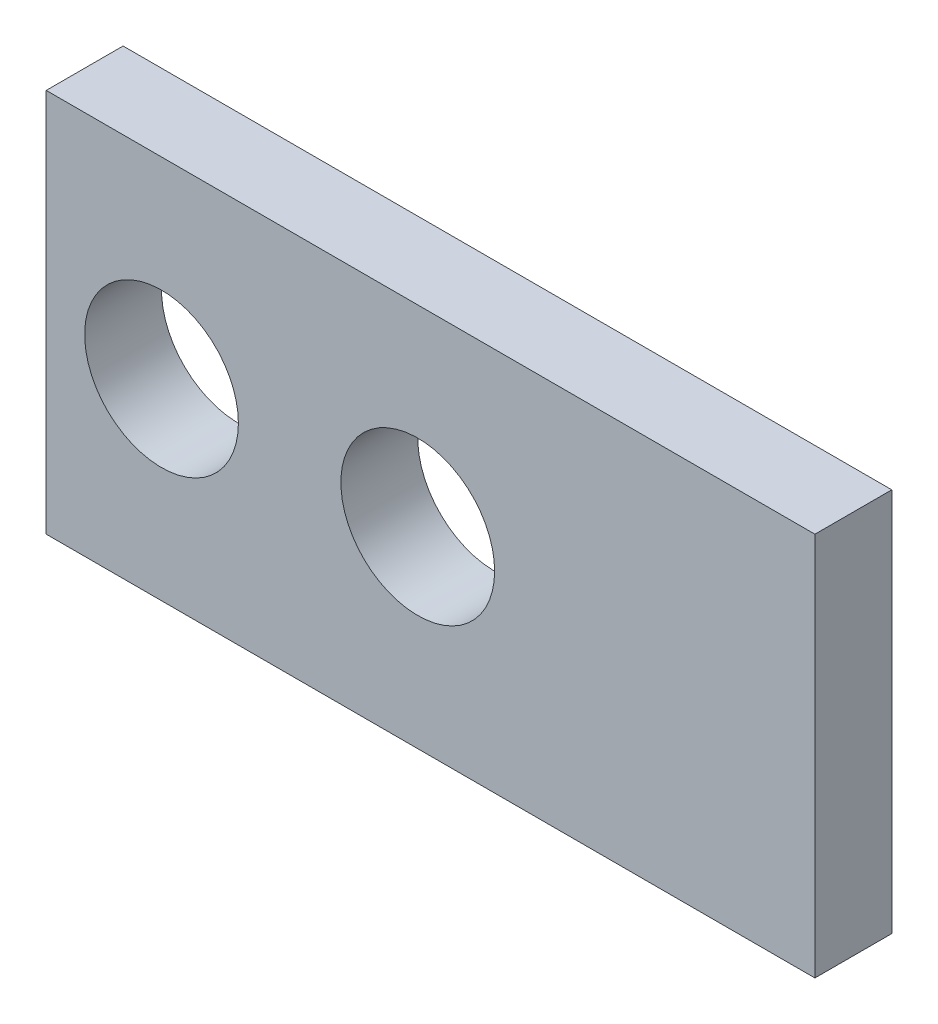
SolidWorks part; units mm, degrees
ref_plane "Piano frontale" through (0, 0, 0) normal (0, 0, 1) x (1, 0, 0)
ref_plane "Piano superiore" through (0, 0, 0) normal (0, 1, 0) x (1, 0, 0)
ref_plane "Piano destro" through (0, 0, 0) normal (1, 0, 0) x (0, 0, -1)
sketch "Sketch1" plane through (0, 0, 0) normal (0, 0, 1) x (1, 0, 0)
  line L1 (-50, -25) -> (50, -25)
  line L2 (-50, -25) -> (-50, 25)
  line L3 (-50, 25) -> (50, 25)
  line L4 (50, -25) -> (50, 25)
  line L5 (-50, -25) -> (50, 25) construction
  line L6 (-50, 25) -> (50, -25) construction
  point P0 (0, 0)
extrude "Boss-Extrude1" add sketch "Sketch1" along normal blind 10
hole_wizard "Ø20.0mm Dowel Slot1" positions "Sketch3" profile "Sketch2" size "Ø20.0" standard "ANSI Metric" slot yes
sketch "Sketch3" plane through (0, 0, 10) normal (0, 0, 1) x (1, 0, 0)
  line L0 (-50, 25) -> (-50, -25) construction
  line L1 (5.5, 0) -> (-5.5, 0) construction
  point P0 (-35, 0)
  dimension "D1" = 15
sketch "Sketch2" plane through (-35, 0, 10) normal (1, 0, 0) x (0, -1, 0)
  line L0 (0, 0) -> (0, 16.0086)
  line L1 (0, 16.0086) -> (10, 10)
  line L2 (10, 10) -> (10, 0)
  line L5 (10, 0) -> (0, 0)
  line L10 (0, 16.0086) -> (-10, 10) construction
  line L11 (0, -6.35) -> (0, 107.95) construction
  dimension "Hole Dia." = 20
  dimension "Hole Depth" = 10
  dimension "Drill Angle" = 118
pattern_linear "LPattern1" count 2 spacing 33.3333 along (1, 0, 0) of "Ø20.0mm Dowel Slot1"
equation "\"D1@LPattern1\"= IIF ( \"D1@Sketch1\" < 75 , 1 , IIF ( \"D1@Sketch1\" < 125 , 2 , 3 ) )'Anzahl der Locher"
equation "\"D3@LPattern1\"= \"D1@Sketch1\" / ( \"D1@LPattern1\" + 1 )'Abstand der Locher"
